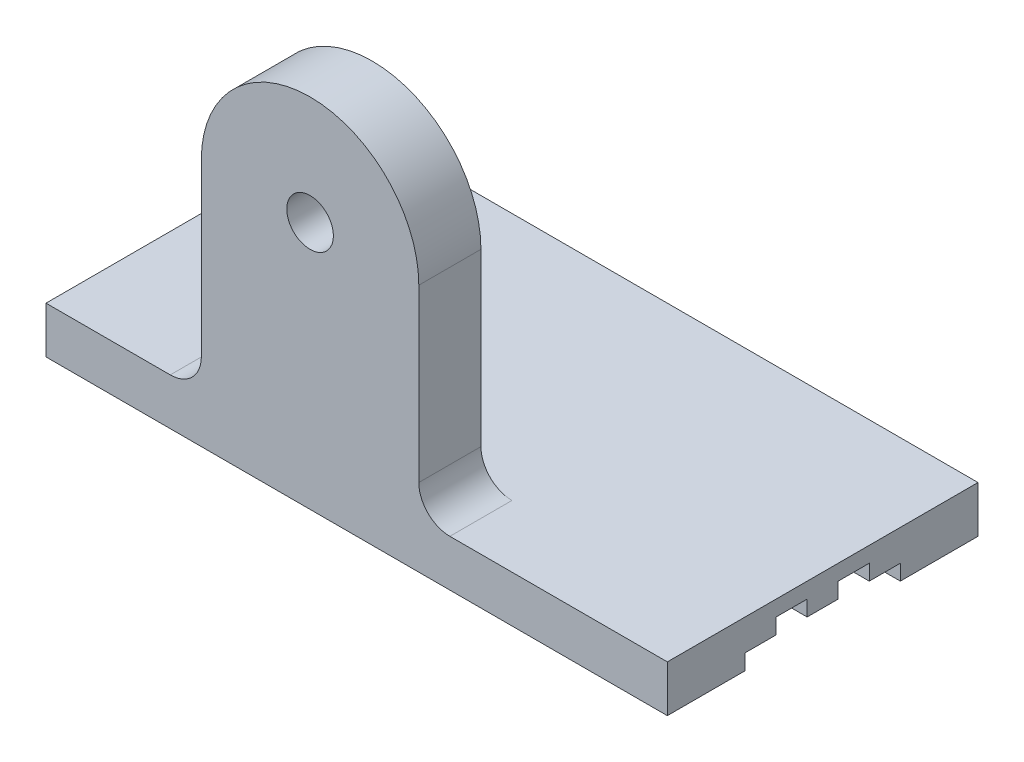
SolidWorks part; units mm, degrees
material "ABS"
ref_plane "정면" through (0, 0, 0) normal (0, 0, 1) x (1, 0, 0)
ref_plane "윗면" through (0, 0, 0) normal (0, 1, 0) x (1, 0, 0)
ref_plane "우측면" through (0, 0, 0) normal (1, 0, 0) x (0, 0, -1)
sketch "스케치1" plane through (0, 0, 0) normal (0, 1, 0) x (1, 0, 0)
  line L1 (0, 0) -> (200, 0)
  line L2 (0, 0) -> (0, 100)
  line L3 (0, 100) -> (200, 100)
  line L4 (200, 0) -> (200, 100)
extrude "보스-돌출1" add sketch "스케치1" along normal blind 15
sketch "스케치2" plane through (0, 0, 0) normal (0, 0, 1) x (1, 0, 0)
  line L0 (0, 0) -> (200, 0) construction
  line L1 (50, 0) -> (120, 0)
  line L2 (50, 0) -> (50, 80)
  line L4 (120, 0) -> (120, 80)
  arc A0 (120, 80) -> (50, 80) centre (85, 80) ccw
  dimension "D4" = 35
  dimension "D1" = 80
  dimension "D2" = 70
  dimension "D3" = 50
extrude "보스-돌출2" add sketch "스케치2" against normal blind 20
sketch "스케치3" plane through (200, 0, 0) normal (1, 0, 0) x (0, 0, -1)
  line L0 (25, 0) -> (25, 5)
  line L1 (0, 0) -> (100, 0) construction
  line L2 (25, 5) -> (35, 5)
  line L3 (35, 5) -> (35, 10)
  line L4 (35, 10) -> (45, 10)
  line L5 (45, 10) -> (45, 5)
  line L6 (45, 5) -> (55, 5)
  line L7 (55, 5) -> (55, 10)
  line L8 (55, 10) -> (65, 10)
  line L9 (65, 10) -> (65, 5)
  line L10 (65, 5) -> (75, 5)
  line L11 (75, 5) -> (75, 0)
  line L12 (75, 0) -> (25, 0)
  dimension "D1" = 5
  dimension "D2" = 25
  dimension "D3" = 10
  dimension "D4" = 5
  dimension "D5" = 10
extrude "컷-돌출2" cut sketch "스케치3" against normal through all contours L12 L0 L2 L3 L4 L5 L6 L7 L8 L9 L10 L11
sketch "스케치4" plane through (0, 0, 0) normal (0, 0, 1) x (1, 0, 0)
  circle A0 centre (85, 80) radius 7.5
  arc A1 (120, 80) -> (50, 80) centre (85, 80) ccw construction
  point P2 (0, 0)
  point P3 (0, 0)
  dimension "D1" = 15
extrude "컷-돌출3" cut sketch "스케치4" against normal through all contours A0
fillet "필렛2" radius 10 2 edges at (50, 15, -10) (120, 15, -10)
